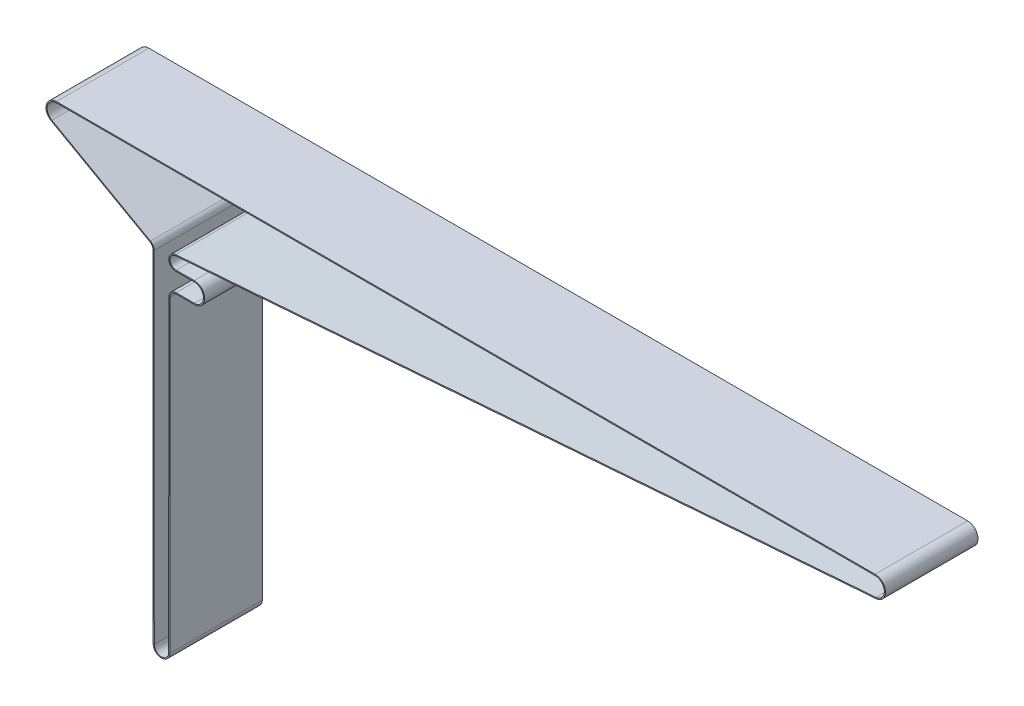
SolidWorks part; units mm, degrees
ref_plane "Front Plane" through (0, 0, 0) normal (0, 0, 1) x (1, 0, 0)
ref_plane "Top Plane" through (0, 0, 0) normal (0, 1, 0) x (1, 0, 0)
ref_plane "Right Plane" through (0, 0, 0) normal (1, 0, 0) x (0, 0, -1)
sketch "Sketch1" plane through (0, 0, 0) normal (0, 0, 1) x (1, 0, 0)
  line L0 (-1124.003, 0) -> (0, 0) construction
  line L1 (-1124.003, 12.7) -> (0, 12.7)
  line L3 (-979.703, -563.9) -> (-979.703, 0) construction
  line L6 (-960.4546, -85.8226) -> (0.9636, -12.6634)
  line L7 (-1130.2196, -11.0744) -> (-994.854, -87.0619)
  line L8 (-989.609, -563.904) -> (-989.797, -95.696)
  line L9 (-959.6609, -105.6059) -> (-934.757, -105.5001)
  line L10 (-934.757, -130.8999) -> (-959.6609, -130.7941)
  line L11 (-969.609, -140.6956) -> (-969.797, -563.9044)
  line L12 (-959.703, -95.7) -> (-959.703, -140.7) construction
  line L13 (-999.703, -95.7) -> (-959.703, -95.7) construction
  arc A0 (-1124.003, 12.7) -> (-1130.2196, -11.0744) centre (-1124.003, 0) ccw
  arc A1 (0.9636, -12.6634) -> (0, 12.7) centre (0, 0) ccw
  arc A2 (-934.757, -105.5001) -> (-934.757, -130.8999) centre (-934.703, -118.2) cw
  arc A3 (-989.609, -563.904) -> (-969.797, -563.9044) centre (-979.703, -563.9) ccw
  arc A4 (-989.797, -95.696) -> (-994.854, -87.0619) centre (-999.703, -95.7) ccw
  arc A5 (-959.6609, -130.7941) -> (-969.609, -140.6956) centre (-959.703, -140.7) ccw
  arc A9 (-959.6609, -105.6059) -> (-960.4546, -85.8226) centre (-959.703, -95.7) cw
  circle A12 centre (-979.703, -563.9) radius 9.906 construction
  circle A13 centre (-959.703, -140.7) radius 9.906 construction
  circle A14 centre (-934.703, -118.2) radius 12.7 construction
  circle A15 centre (-959.703, -95.7) radius 9.906 construction
  circle A16 centre (-999.703, -95.7) radius 9.906 construction
  point P23 (-949.7393, -44.9)
  dimension "D3" = 9.906
  dimension "D7" = 9.906
  dimension "D4" = 9.906
  dimension "D2" = 12.7
  dimension "D8" = 9.906
  dimension "D15" = 19.812
  dimension "D16" = 19.812
  dimension "D17" = 19.812
  dimension "D18" = 25.4
  dimension "D1" = 1124.003
  dimension "D6" = 563.9
  dimension "D5" = 144.3
  dimension "D9" = 20
  dimension "D10" = 20
  dimension "D11" = 45
  dimension "D12" = 45
  dimension "D14" = 95.7
  dimension "D13" = 22.5
extrude "Extrude-Thin1" add sketch "Sketch1" along normal mid plane 127 thin contours L1 A1 L6 A9 L9 A2 L10 A5 L11 A3 L8 A4 L7 A0 thin type one direction wall 1.524
equation "\"D7@Sketch1\"=\"D4@Sketch1\""
equation "\"D2@Sketch1\"=.5in"
equation "\"D8@Sketch1\"= \"D4@Sketch1\""
